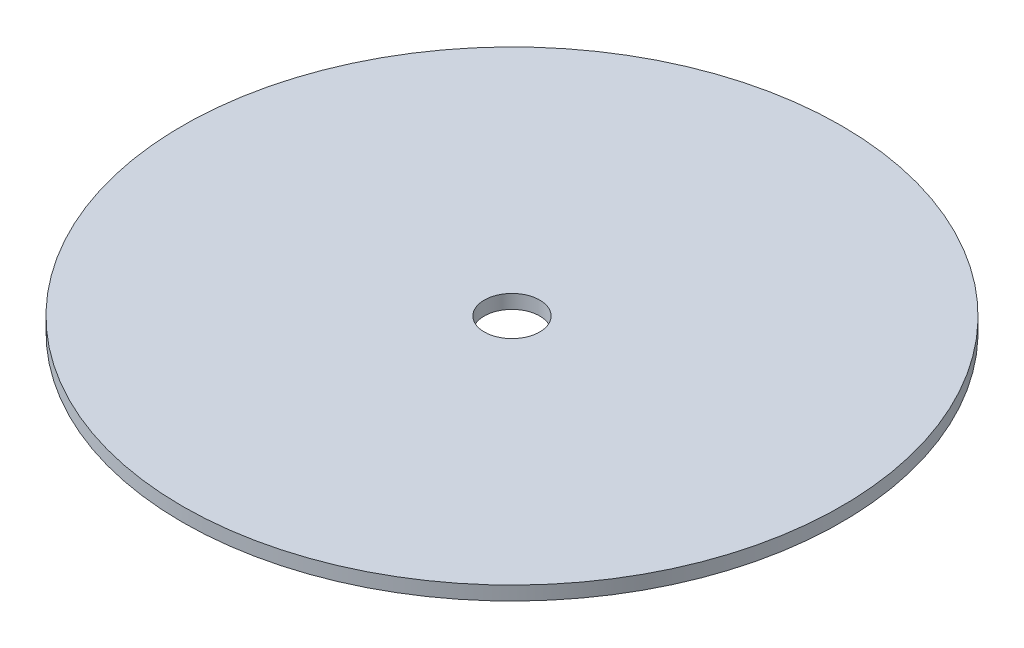
SolidWorks part; units mm, degrees
material "E-Glass Fiber"
ref_plane "Front Plane" through (0, 0, 0) normal (0, 0, 1) x (1, 0, 0)
ref_plane "Top Plane" through (0, 0, 0) normal (0, 1, 0) x (1, 0, 0)
ref_plane "Right Plane" through (0, 0, 0) normal (1, 0, 0) x (0, 0, -1)
sketch "Sketch1" plane through (0, 0, 0) normal (0, 1, 0) x (1, 0, 0)
  circle A0 centre (0, 0) radius 75.565
  dimension "D1" = 151.13
extrude "Boss-Extrude1" add sketch "Sketch1" along normal blind 3.175
sketch "Sketch3" plane through (0, 3.175, 0) normal (0, 1, 0) x (1, 0, 0)
  circle A0 centre (0, 0) radius 6.35
  dimension "D1" = 12.7
extrude "Cut-Extrude1" cut sketch "Sketch3" against normal through all and the other way through all
